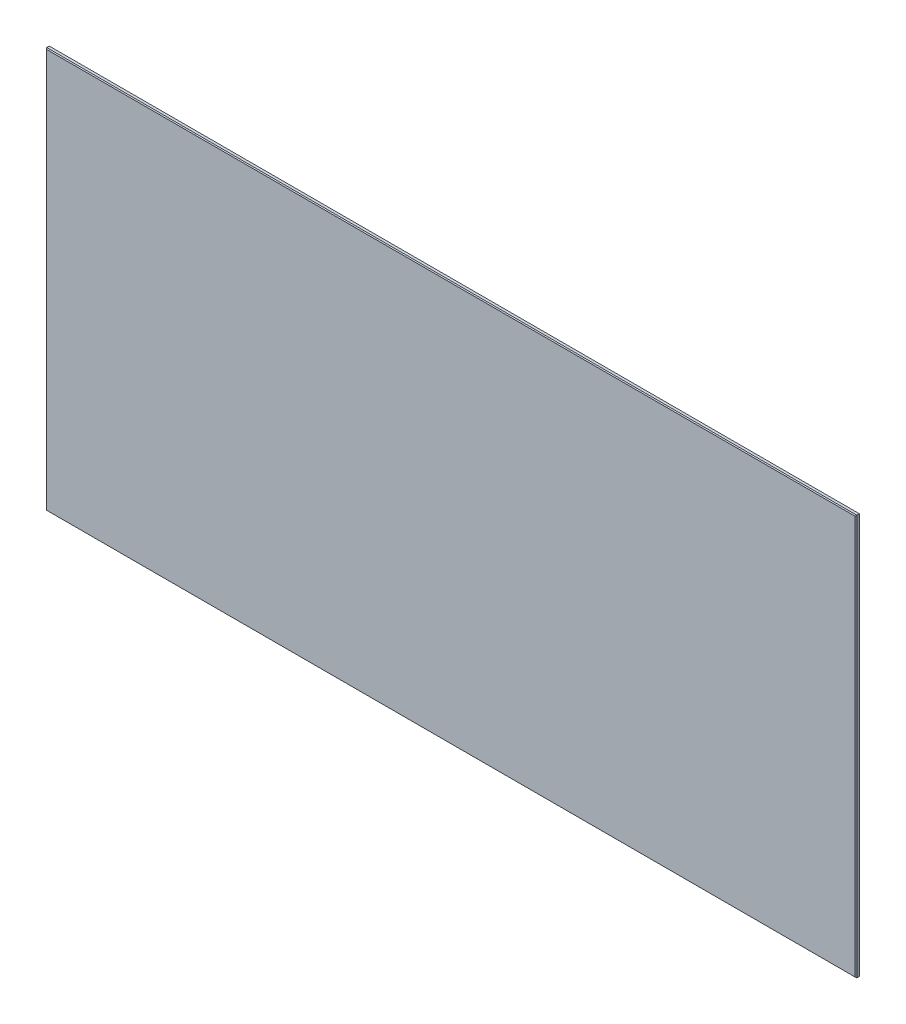
SolidWorks part; units mm, degrees
material "Glass"
ref_plane "Front Plane" through (0, 0, 0) normal (0, 0, 1) x (1, 0, 0)
ref_plane "Top Plane" through (0, 0, 0) normal (0, 1, 0) x (1, 0, 0)
ref_plane "Right Plane" through (0, 0, 0) normal (1, 0, 0) x (0, 0, -1)
sketch "Sketch2" plane through (0, 0, 0) normal (0, 0, 1) x (1, 0, 0)
  line L1 (603.25, -298.45) -> (-603.25, -298.45)
  line L2 (603.25, -298.45) -> (603.25, 298.45)
  line L3 (603.25, 298.45) -> (-603.25, 298.45)
  line L4 (-603.25, -298.45) -> (-603.25, 298.45)
  line L5 (603.25, -298.45) -> (-603.25, 298.45) construction
  line L6 (603.25, 298.45) -> (-603.25, -298.45) construction
  point P0 (0, 0)
  dimension "D1" = 596.9
  dimension "D2" = 1206.5
sketch "Sketch1" plane through (0, 0, 0) normal (1, 0, 0) x (0, 0, -1)
  line L7 (3.175, -297.18) -> (3.175, 297.18)
  line L8 (1.905, 298.45) -> (-1.905, 298.45)
  line L9 (-3.175, 297.18) -> (-3.175, -297.18)
  line L18 (3.175, 297.18) -> (1.905, 298.45)
  line L19 (-1.905, 298.45) -> (-3.175, 297.18)
  line L20 (-1.905, -298.45) -> (1.905, -298.45)
  line L21 (-3.175, -297.18) -> (-1.905, -298.45)
  line L22 (1.905, -298.45) -> (3.175, -297.18)
  point P4 (0, 298.45)
  point P5 (0, -298.45)
  point P9 (3.175, 298.45)
  point P10 (-3.175, 298.45)
  point P15 (-3.175, -298.45)
  point P18 (3.175, -298.45)
  dimension "D1" = 6.35
  dimension "D18" = 1.27
  dimension "D19" = 1.27
  dimension "D20" = 1.27
  dimension "D21" = 1.27
extrude "Boss-Extrude1" add sketch "Sketch1" along normal up to vertex (603.25 mm away) and the other way up to vertex (603.25 mm away) contours L9 L21 L20 L22 L7 L18 L8 L19 up to point (603.25, 298.45, 0) other way up to point (-603.25, 298.45, 0)
chamfer "Chamfer1" distance 1.27 angle 45 4 edges at (-603.25, 0, -3.175) (-603.25, 0, 3.175) (603.25, 0, -3.175) (603.25, 0, 3.175)
